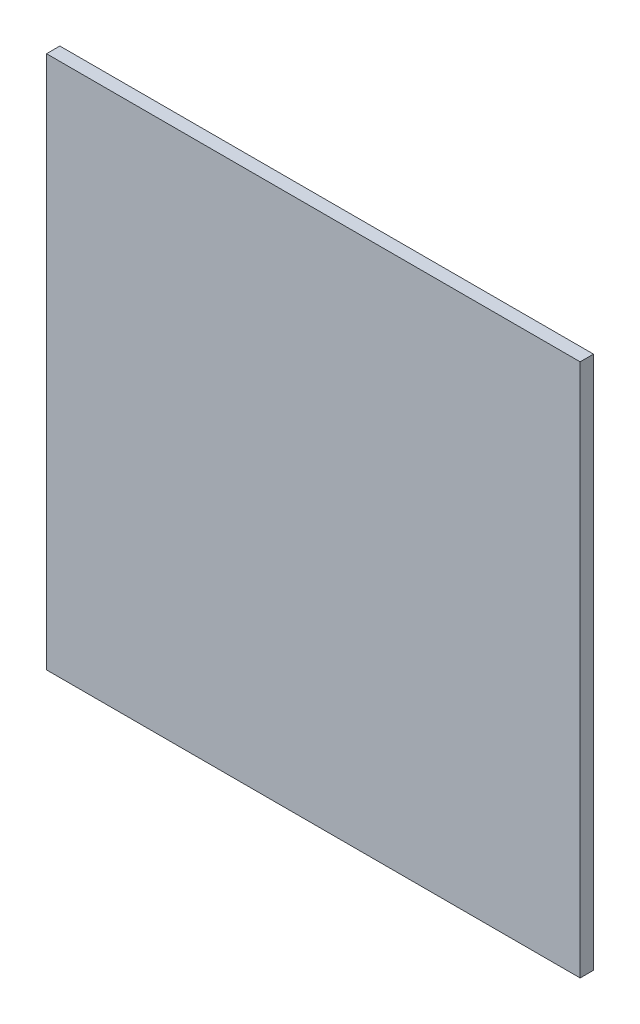
SolidWorks part; units mm, degrees
ref_plane "Front Plane" through (0, 0, 0) normal (0, 0, 1) x (1, 0, 0)
ref_plane "Top Plane" through (0, 0, 0) normal (0, 1, 0) x (1, 0, 0)
ref_plane "Right Plane" through (0, 0, 0) normal (1, 0, 0) x (0, 0, -1)
sketch "Sketch1" plane through (0, 0, 0) normal (0, 0, 1) x (1, 0, 0)
  line L1 (118.1584, 84.8584) -> (-281.8416, 84.8584)
  line L2 (118.1584, 84.8584) -> (118.1584, -315.1416)
  line L3 (118.1584, -315.1416) -> (-281.8416, -315.1416)
  line L4 (-281.8416, 84.8584) -> (-281.8416, -315.1416)
  line L5 (118.1584, 84.8584) -> (-281.8416, -315.1416) construction
  line L6 (118.1584, -315.1416) -> (-281.8416, 84.8584) construction
  point P0 (-81.8416, -115.1416)
  dimension "D1" = 400
  dimension "D2" = 400
extrude "Boss-Extrude1" add sketch "Sketch1" along normal blind 10
equation "\"mat\"=\"mat@V1.assembly\""
equation "\"TXD1@Scheme2\" =\"mat\""
